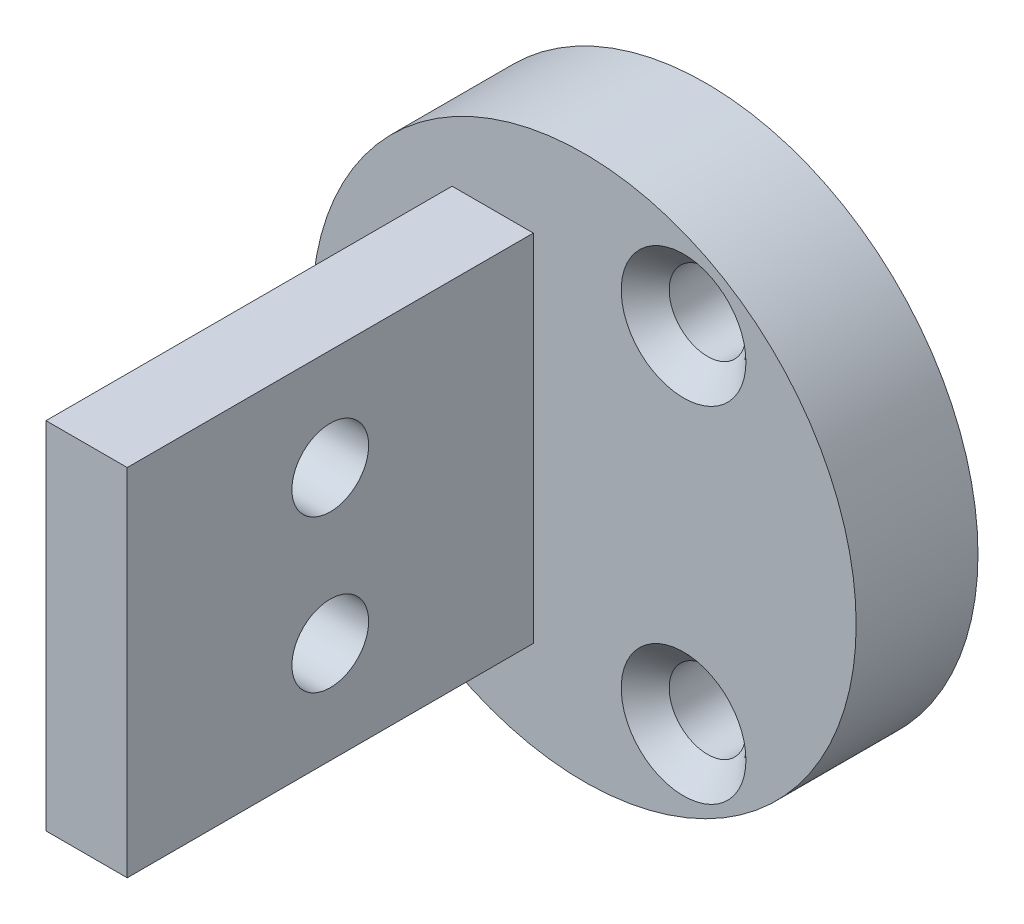
SolidWorks part; units mm, degrees
ref_plane "Front Plane" through (0, 0, 0) normal (0, 0, 1) x (1, 0, 0)
ref_plane "Top Plane" through (0, 0, 0) normal (0, 1, 0) x (1, 0, 0)
ref_plane "Right Plane" through (0, 0, 0) normal (1, 0, 0) x (0, 0, -1)
sketch "Sketch2" plane through (0, 0, 0) normal (0, 0, 1) x (1, 0, 0)
  circle A0 centre (0, 0) radius 8.509
  dimension "D1" = 17.018
extrude "Boss-Extrude1" add sketch "Sketch2" along normal blind 3.81
ref_plane "Plane1" through (0, 0, 3.81) normal (0, 0, 1) x (1, 0, 0)
sketch "Sketch3" plane through (0, 0, 3.81) normal (0, 0, 1) x (1, 0, 0)
  line L0 (-8.509, 0) -> (8.509, 0) construction
  circle A0 centre (0, 0) radius 6.223 construction
  circle A2 centre (0, 0) radius 8.509 construction
  circle A3 centre (-6.223, 0) radius 1.143
  circle A4 centre (3.1115, 5.3893) radius 1.143
  circle A5 centre (3.1115, -5.3893) radius 1.143
  point P16 (0, 0)
  dimension "D1" = 12.446
  dimension "D2" = 2.286
  dimension "D4" = 5.3893
  dimension "D5" = 3.1115
  dimension "D3" = 3
sketch "Sketch4" plane through (0, 0, 3.81) normal (0, 0, 1) x (1, 0, 0)
  line L1 (-4.1275, 5.5562) -> (-1.5875, 5.5562)
  line L2 (-4.1275, 5.5562) -> (-4.1275, -5.5562)
  line L3 (-4.1275, -5.5562) -> (-1.5875, -5.5562)
  line L4 (-1.5875, 5.5562) -> (-1.5875, -5.5562)
  dimension "D1" = 2.54
  dimension "D2" = 11.1125
  dimension "D3" = 1.5875
  dimension "D4" = 5.5562
extrude "Boss-Extrude2" add sketch "Sketch4" along normal blind 12.7
sketch "Sketch5" plane through (-1.5875, 0, 0) normal (1, 0, 0) x (0, 0, -1)
  line L0 (-16.51, -5.5562) -> (-16.51, 5.5562) construction
  line L1 (-16.51, -5.5562) -> (-3.81, -5.5562) construction
  line L2 (-16.51, 5.5562) -> (-3.81, 5.5562) construction
  circle A0 centre (-10.16, 2.3813) radius 1.143
  circle A1 centre (-10.16, -2.3812) radius 1.143
  dimension "D1" = 2.286
  dimension "D2" = 2.286
  dimension "D3" = 6.35
  dimension "D4" = 6.35
  dimension "D5" = 3.175
  dimension "D6" = 3.175
hole_wizard "M2 Clearance Hole1" positions "Sketch6" profile "Sketch7" hole size "M2" standard "ANSI Metric" end condition through all
sketch "Sketch6" plane through (0, 0, 3.81) normal (0, 0, 1) x (1, 0, 0)
  point P0 (-6.223, 0)
  point P3 (3.1115, 5.3893)
  point P6 (3.1115, -5.3893)
sketch "Sketch7" plane through (-6.223, 0, 3.81) normal (1, 0, 0) x (0, -1, 0)
  line L0 (0, 0) -> (0, 3.81)
  line L1 (0, 3.81) -> (1.2, 3.81)
  line L2 (1.2, 3.81) -> (1.2, 0)
  line L5 (1.2, 0) -> (0, 0)
  line L11 (0, -6.35) -> (0, 107.95) construction
  dimension "Thru Hole Dia." = 2.4
  dimension "Thru Hole Depth" = 3.81
hole_wizard "M2 Clearance Hole2" positions "Sketch8" profile "Sketch9" hole size "M2" standard "ANSI Metric" end condition through all
sketch "Sketch8" plane through (-1.5875, 0, 0) normal (1, 0, 0) x (0, 0, -1)
  point P0 (-10.16, -2.3812)
  point P3 (-10.16, 2.3813)
sketch "Sketch9" plane through (-1.5875, -2.3812, 10.16) normal (0, 1, 0) x (0, 0, -1)
  line L0 (0, 0) -> (0, 6.9215)
  line L1 (0, 6.9215) -> (1.2, 6.9215)
  line L2 (1.2, 6.9215) -> (1.2, 0)
  line L5 (1.2, 0) -> (0, 0)
  line L11 (0, -6.35) -> (0, 107.95) construction
  dimension "Thru Hole Dia." = 2.4
  dimension "Thru Hole Depth" = 6.9215
chamfer "Chamfer1" distance 0.75 angle 45 1 edges at (4.3115, -5.3893, 3.81)
chamfer "Chamfer2" distance 0.75 angle 45 1 edges at (4.3115, 5.3893, 3.81)
chamfer "Chamfer3" distance 0.75 angle 45 1 edges at (-5.023, 0, 3.81)
